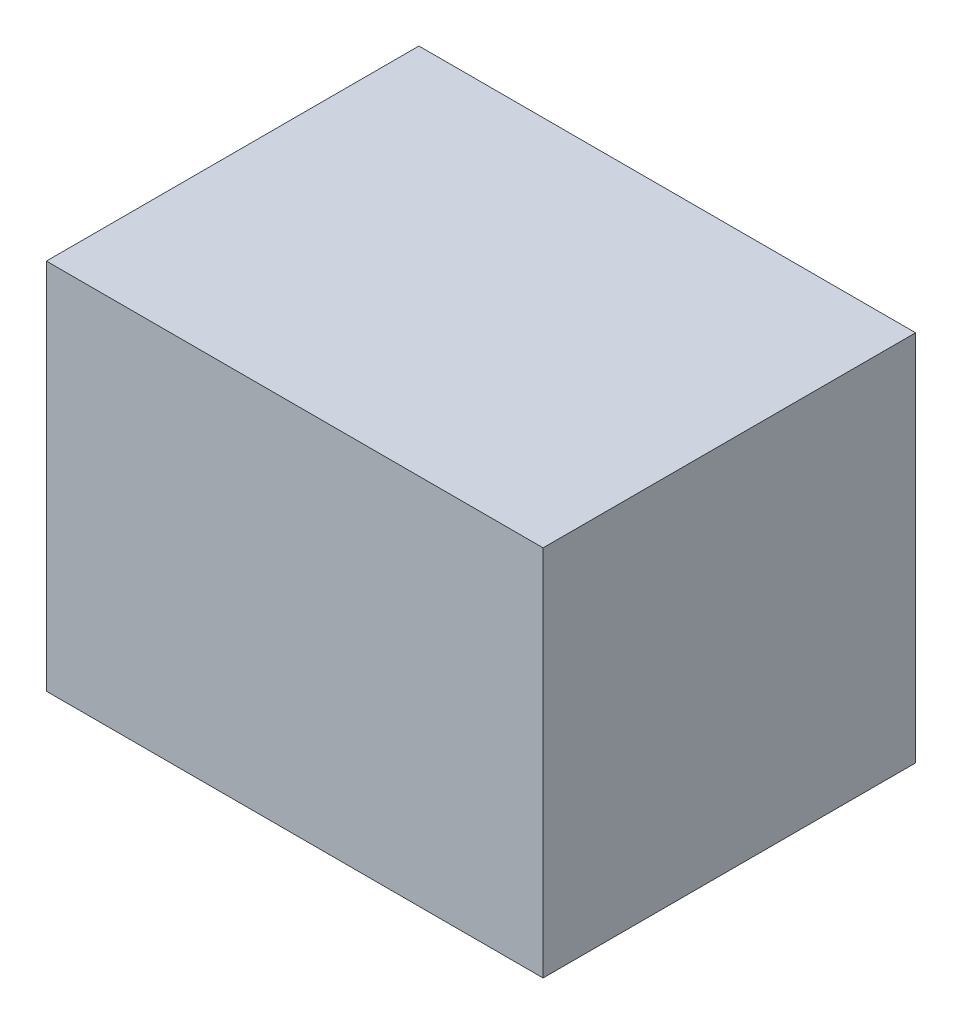
SolidWorks part; units mm, degrees
ref_plane "Front Plane" through (0, 0, 0) normal (0, 0, 1) x (1, 0, 0)
ref_plane "Top Plane" through (0, 0, 0) normal (0, 1, 0) x (1, 0, 0)
ref_plane "Right Plane" through (0, 0, 0) normal (1, 0, 0) x (0, 0, -1)
sketch "Sketch2" plane through (0, 0, 0) normal (0, 0, 1) x (1, 0, 0)
  line L1 (0, 0) -> (4, 0)
  line L2 (0, 0) -> (0, 3)
  line L3 (0, 3) -> (4, 3)
  line L4 (4, 0) -> (4, 3)
  dimension "D1" = 4
  dimension "D2" = 3
extrude "Boss-Extrude1" add sketch "Sketch2" along normal blind 3
